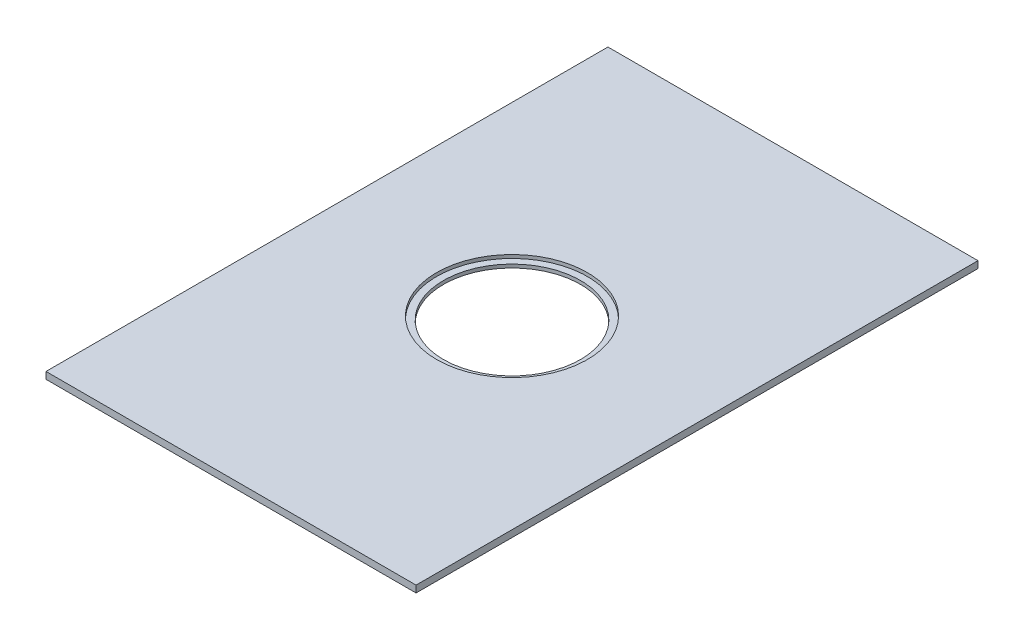
SolidWorks part; units mm, degrees
material "PVC Rigid"
ref_plane "Front Plane" through (0, 0, 0) normal (0, 0, 1) x (1, 0, 0)
ref_plane "Top Plane" through (0, 0, 0) normal (0, 1, 0) x (1, 0, 0)
ref_plane "Right Plane" through (0, 0, 0) normal (1, 0, 0) x (0, 0, -1)
sketch "Sketch1" plane through (0, 0, 0) normal (0, 1, 0) x (1, 0, 0)
  line L0 (54, 82) -> (54, -82)
  line L7 (54, -82) -> (-54, -82)
  line L8 (-54, -82) -> (-54, 82)
  line L9 (-54, 82) -> (54, 82)
  point P0 (54, 0)
extrude "Boss-Extrude1" add sketch "Sketch1" against normal blind 2
sketch "Sketch2" plane through (0, 0, 0) normal (0, 1, 0) x (1, 0, 0)
  circle A0 centre (0, 0) radius 22
extrude "Cut-Extrude1" cut sketch "Sketch2" against normal blind 1
sketch "Sketch3" plane through (0, -1, 0) normal (0, 1, 0) x (1, 0, 0)
  circle A0 centre (0, 0) radius 20
extrude "Cut-Extrude2" cut sketch "Sketch3" against normal through all
